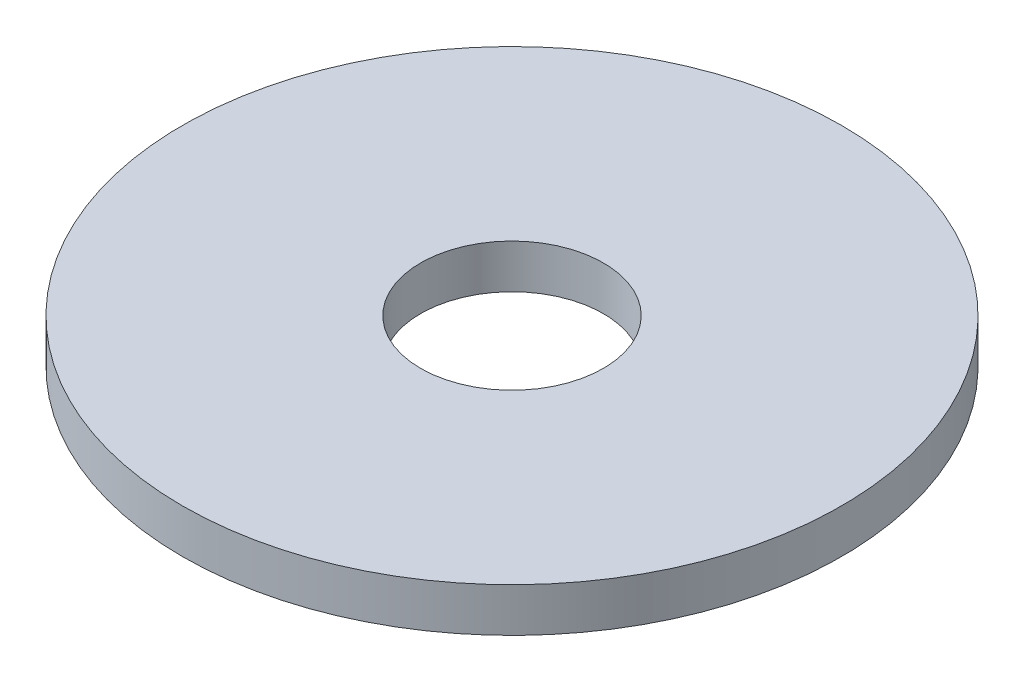
SolidWorks part; units mm, degrees
ref_plane "Front Plane" through (0, 0, 0) normal (0, 0, 1) x (1, 0, 0)
ref_plane "Top Plane" through (0, 0, 0) normal (0, 1, 0) x (1, 0, 0)
ref_plane "Right Plane" through (0, 0, 0) normal (1, 0, 0) x (0, 0, -1)
sketch "Sketch1" plane through (0, 0, 0) normal (0, 1, 0) x (1, 0, 0)
  circle A0 centre (0, 0) radius 9.525
  circle A1 centre (0, 0) radius 2.6416
  dimension "D1" = 19.05
  dimension "D2" = 5.2832
extrude "Boss-Extrude1" add sketch "Sketch1" along normal blind 1.27
